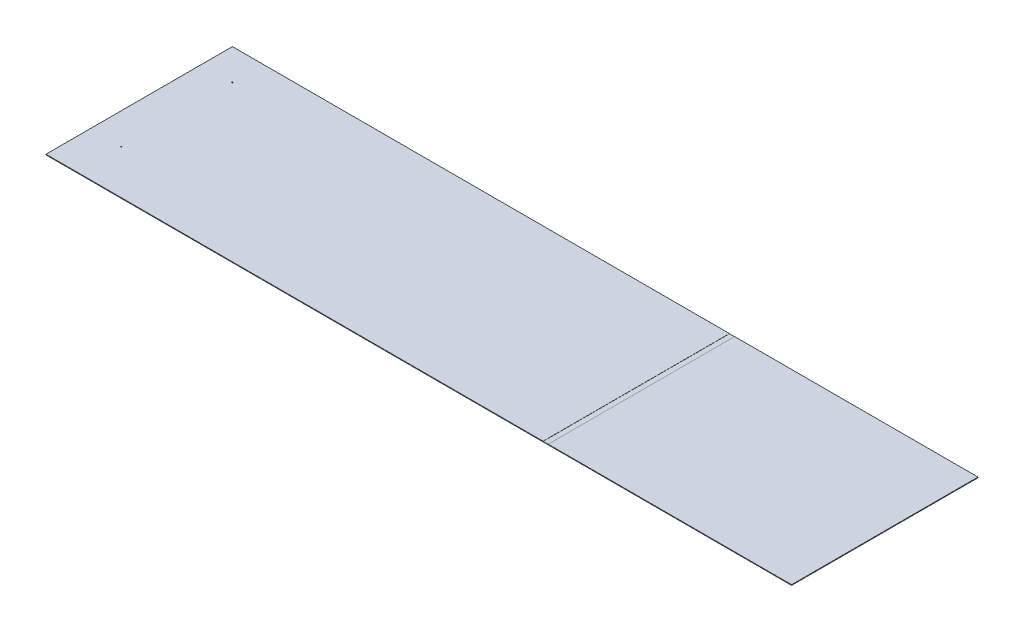
SolidWorks part; units mm, degrees
ref_plane "Front Plane" through (0, 0, 0) normal (0, 0, 1) x (1, 0, 0)
ref_plane "Top Plane" through (0, 0, 0) normal (0, 1, 0) x (1, 0, 0)
ref_plane "Right Plane" through (0, 0, 0) normal (1, 0, 0) x (0, 0, -1)
sketch "Sketch1" plane through (0, 0, 0) normal (0, 1, 0) x (1, 0, 0)
  line L1 (-1408.6799, 803.6927) -> (2248.9201, 803.6927)
  line L2 (-1408.6799, 803.6927) -> (-1408.6799, -110.7073)
  line L3 (-1408.6799, -110.7073) -> (2248.9201, -110.7073)
  line L4 (2248.9201, 803.6927) -> (2248.9201, -110.7073)
  dimension "D1" = 914.4
  dimension "D2" = 3657.6
extrude "Boss-Extrude1" add sketch "Sketch1" along normal blind 3.175
sketch "Sketch2" plane through (0, 3.175, 0) normal (0, 1, 0) x (1, 0, 0)
  line L0 (2248.9201, 803.6927) -> (-1408.6799, 803.6927) construction
  line L1 (-1408.6799, 803.6927) -> (-1408.6799, -110.7073) construction
  circle A0 centre (-1256.2799, 651.2927) radius 2.5797
  circle A1 centre (-1256.2799, 105.1927) radius 2.5797
  point P1 (-1256.2799, 651.2927)
  point P2 (-1256.2799, 105.1927)
  point P6 (0, 0)
  dimension "D2" = 5.1594
  dimension "D3" = 5.1594
  dimension "D1" = 546.1
  dimension "D4" = 152.4
  dimension "D5" = 152.4
extrude "Cut-Extrude1" cut sketch "Sketch2" against normal blind 3.175
sketch "Sketch3" plane through (0, 3.175, 0) normal (0, 1, 0) x (1, 0, 0)
  line L0 (-1408.6799, 803.6927) -> (2248.9201, 803.6927) construction
  line L1 (1029.7201, 803.6927) -> (1055.1201, 803.6927)
  line L2 (1029.7201, 803.6927) -> (1029.7201, -110.7073)
  line L3 (1029.7201, -110.7073) -> (1055.1201, -110.7073)
  line L4 (1055.1201, 803.6927) -> (1055.1201, -110.7073)
  line L5 (-1408.6799, -110.7073) -> (2248.9201, -110.7073) construction
  line L6 (-1408.6799, 803.6927) -> (-1408.6799, -110.7073) construction
  dimension "D1" = 0
  dimension "D2" = 0
  dimension "D3" = 25.4
  dimension "D4" = 2438.4
extrude "Cut-Extrude2" cut sketch "Sketch3" against normal blind 0.7937
